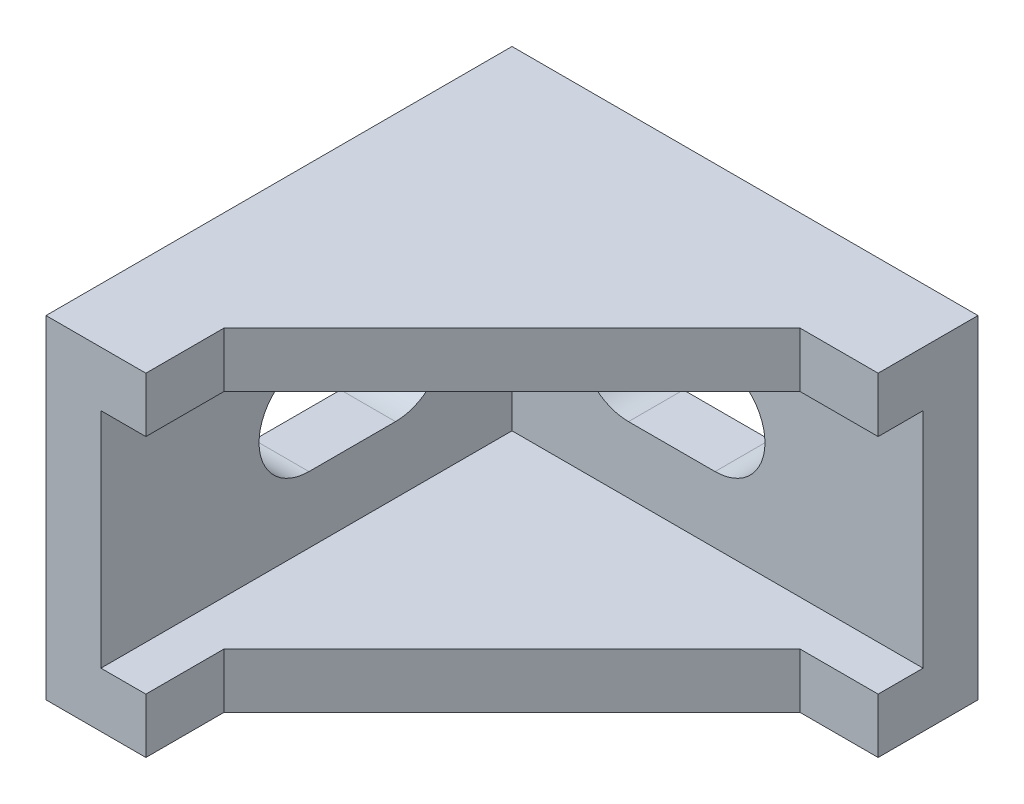
SolidWorks part; units mm, degrees
ref_plane "Front Plane" through (0, 0, 0) normal (0, 0, 1) x (1, 0, 0)
ref_plane "Top Plane" through (0, 0, 0) normal (0, 1, 0) x (1, 0, 0)
ref_plane "Right Plane" through (0, 0, 0) normal (1, 0, 0) x (0, 0, -1)
sketch "Sketch1" plane through (0, 0, 0) normal (1, 0, 0) x (0, 0, -1)
  line L0 (12.5, 10.28) -> (17.7, 10.28) construction
  line L1 (0, 0) -> (28, 0)
  line L2 (0, 0) -> (0, 20)
  line L3 (0, 20) -> (28, 20)
  line L4 (28, 0) -> (28, 20)
  line L5 (12.5, 13.28) -> (17.7, 13.28)
  line L6 (12.5, 7.28) -> (17.7, 7.28)
  arc A0 (12.5, 13.28) -> (12.5, 7.28) centre (12.5, 10.28) ccw
  arc A1 (17.7, 7.28) -> (17.7, 13.28) centre (17.7, 10.28) ccw
  point P7 (15.1, 10.28)
  dimension "D5" = 10.3
  dimension "D1" = 28
  dimension "D2" = 20
  dimension "D3" = 6
  dimension "D4" = 5.2
extrude "Boss-Extrude1" add sketch "Sketch1" along normal blind 3.3
ref_plane "Plane1" through (14, 0, -14) normal (-0.7071, 0, 0.7071) x (0, 1, 0)
mirror "Mirror1" about plane through (14, 0, -14) normal (-0.7071, 0, 0.7071) of "Boss-Extrude1"
ref_plane "Plane2" through (0, 10, 0) normal (0, 1, 0) x (1, 0, 0)
sketch "Sketch2" plane through (0, 10, 0) normal (0, 1, 0) x (1, 0, 0)
  line L0 (3.3, 0) -> (6, 0)
  line L1 (6, 0) -> (6, 4.7)
  line L2 (28, 24.7) -> (28, 22)
  line L3 (28, 22) -> (23.3, 22)
  line L4 (23.3, 22) -> (6, 4.7)
  line L5 (3.3, 0) -> (3.3, 24.7)
  line L6 (3.3, 24.7) -> (28, 24.7)
  dimension "D1" = 6
  dimension "D2" = 6
  dimension "D3" = 4.7
  dimension "D4" = 4.7
extrude "Boss-Extrude2" add sketch "Sketch2" along normal mid plane 20
sketch "Sketch3" plane through (0, 0, 0) normal (0, 0, 1) x (1, 0, 0)
  line L0 (0, 20) -> (0, 0) construction
  line L1 (3.3, 16.7) -> (28, 16.7)
  line L2 (3.3, 16.7) -> (3.3, 3.3)
  line L3 (3.3, 3.3) -> (28, 3.3)
  line L4 (28, 16.7) -> (28, 3.3)
  line L5 (28, 20) -> (28, 0) construction
  line L6 (6, 20) -> (23.3, 20) construction
  line L7 (6, 0) -> (23.3, 0) construction
  dimension "D1" = 3.3
  dimension "D2" = 0
  dimension "D3" = 3.3
  dimension "D4" = 3.3
extrude "Cut-Extrude1" cut sketch "Sketch3" against normal blind 24.7
